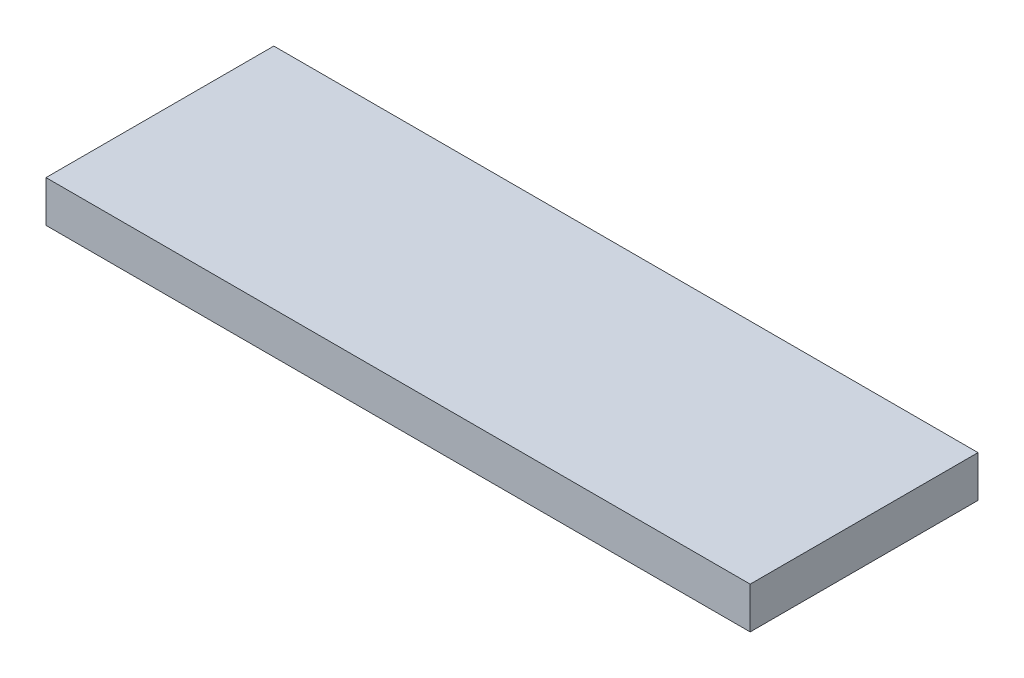
SolidWorks part; units mm, degrees
ref_plane "Front Plane" through (0, 0, 0) normal (0, 0, 1) x (1, 0, 0)
ref_plane "Top Plane" through (0, 0, 0) normal (0, 1, 0) x (1, 0, 0)
ref_plane "Right Plane" through (0, 0, 0) normal (1, 0, 0) x (0, 0, -1)
sketch "Sketch1" plane through (0, 0, 0) normal (0, 1, 0) x (1, 0, 0)
  line L1 (-96.0674, 17.8652) -> (73.9326, 17.8652)
  line L2 (-96.0674, 17.8652) -> (-96.0674, -37.1348)
  line L3 (-96.0674, -37.1348) -> (73.9326, -37.1348)
  line L4 (73.9326, 17.8652) -> (73.9326, -37.1348)
  dimension "D1" = 55
  dimension "D2" = 170
extrude "Boss-Extrude1" add sketch "Sketch1" along normal blind 10
